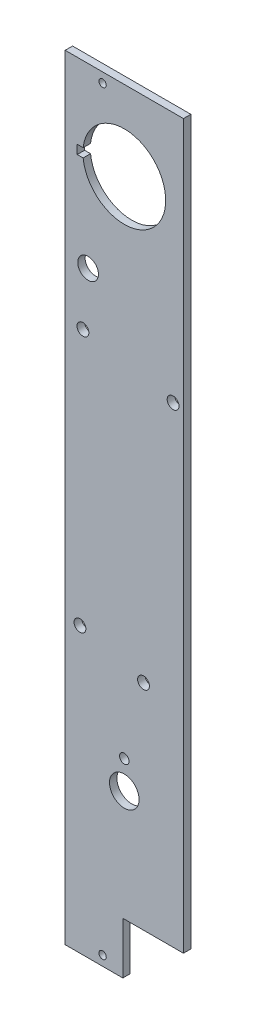
SolidWorks part; units mm, degrees
ref_plane "Front Plane" through (0, 0, 0) normal (0, 0, 1) x (1, 0, 0)
ref_plane "Top Plane" through (0, 0, 0) normal (0, 1, 0) x (1, 0, 0)
ref_plane "Right Plane" through (0, 0, 0) normal (1, 0, 0) x (0, 0, -1)
sketch "Sketch1" plane through (0, 0, 0) normal (0, 0, 1) x (1, 0, 0)
  line L0 (3.8, 262) -> (3.8, 0) construction
  line L1 (0, 0) -> (40, 0)
  line L2 (0, 0) -> (0, 262)
  line L3 (0, 262) -> (40, 262)
  line L4 (40, 0) -> (40, 262)
  line L5 (7.6, 262) -> (7.6, 0) construction
  line L6 (40, 4.2) -> (0, 4.2) construction
  line L8 (40, 18.75) -> (0, 18.75) construction
  line L9 (0, 243.4) -> (40, 243.4) construction
  line L10 (12.65, 262) -> (12.65, 0) construction
  circle A0 centre (12.65, 258.7) radius 1.25
  circle A1 centre (12.65, 3.3) radius 1.25
extrude "Boss-Extrude1" add sketch "Sketch1" along normal blind 2.5
sketch "Sketch2" plane through (0, 0, 2.5) normal (0, 0, 1) x (1, 0, 0)
  line L0 (20, 262) -> (20, 0) construction
  line L1 (40, 262) -> (0, 262) construction
  line L2 (0, 0) -> (40, 0) construction
  line L3 (6.0806, 233.4978) -> (4.0806, 233.4978)
  line L4 (4.0806, 233.4978) -> (4.0806, 236.4978)
  line L5 (4.0806, 236.4978) -> (6.0806, 236.4978)
  circle A0 centre (20, 234.9978) radius 14 construction
  circle A1 centre (20, 55.0048) radius 5
  arc A2 (6.0806, 233.4978) -> (6.0806, 236.4978) centre (20, 234.9978) ccw
  circle A3 centre (20, 64.5048) radius 1.6
  circle A4 centre (5, 96) radius 2
  circle A5 centre (26.5, 90) radius 2
  circle A6 centre (36.5, 177) radius 2
  circle A7 centre (6, 183.25) radius 2
  circle A8 centre (7.75, 202) radius 3.5
extrude "Cut-Extrude1" cut sketch "Sketch2" against normal through all
sketch "Sketch3" plane through (0, 0, 2.5) normal (0, 0, 1) x (1, 0, 0)
  line L1 (40, 0) -> (19.5, 0)
  line L2 (40, 0) -> (40, 17.5)
  line L3 (40, 17.5) -> (19.5, 17.5)
  line L4 (19.5, 0) -> (19.5, 17.5)
extrude "Cut-Extrude2" cut sketch "Sketch3" against normal through all
